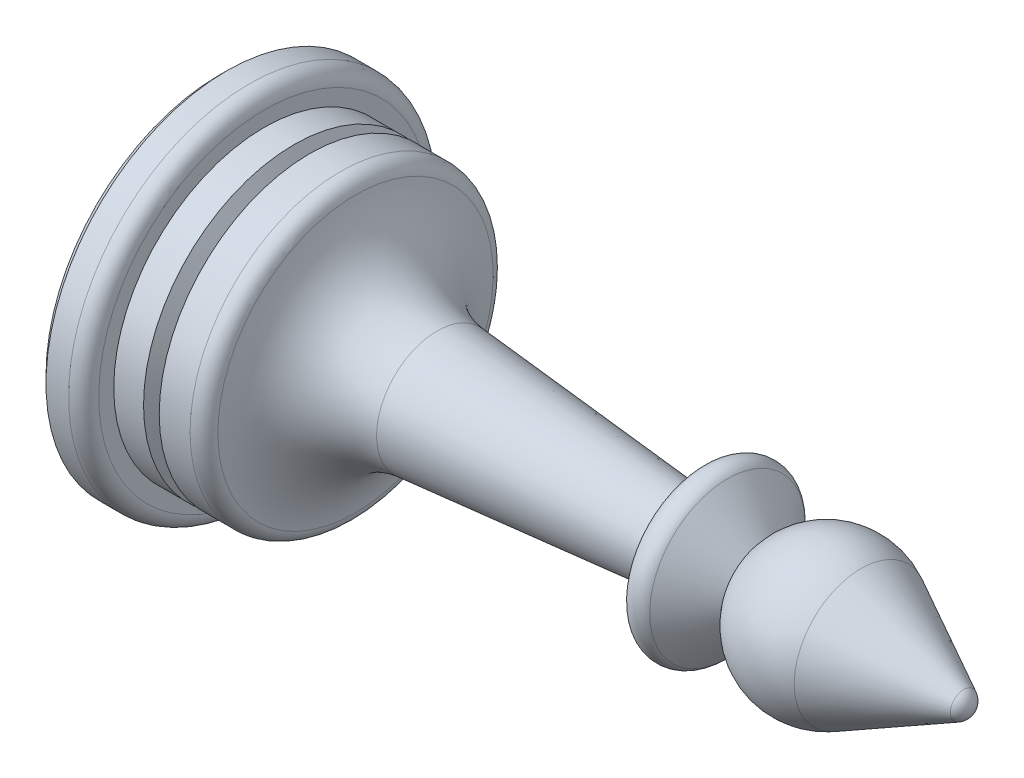
SolidWorks part; units mm, degrees
ref_plane "Front Plane" through (0, 0, 0) normal (0, 0, 1) x (1, 0, 0)
ref_plane "Top Plane" through (0, 0, 0) normal (0, 1, 0) x (1, 0, 0)
ref_plane "Right Plane" through (0, 0, 0) normal (1, 0, 0) x (0, 0, -1)
sketch "Sketch1" plane through (0, 0, 0) normal (0, 0, 1) x (1, 0, 0)
  line L0 (0, 0) -> (0, 11.5)
  line L1 (0.5, 12) -> (2, 12)
  line L2 (3, 11) -> (3, 10)
  line L3 (3, 10) -> (8.0718, 10)
  line L4 (14.4805, 4.0225) -> (32, 2.5)
  line L5 (32, 2.5) -> (32, 4.5195)
  line L6 (33.766, 5.1623) -> (36, 2.5)
  line L7 (0, 0) -> (50, 0)
  line L8 (0, 0) -> (-16.2845, 0) construction
  line L9 (50, 0) -> (50, -26.6806) construction
  line L10 (36, 2.5) -> (36, 27.3883) construction
  line L11 (36, 2.5) -> (48.7777, 27.0457) construction
  line L12 (36, 2.5) -> (23.2223, 27.0457) construction
  line L13 (23.2223, 27.0457) -> (48.7777, 27.0457) construction
  line L14 (0, 11.5) -> (0.5, 12)
  line L15 (42.637, 4.436) -> (49.4614, 0.8872)
  arc A0 (9.0615, 9.1429) -> (14.4805, 4.0225) centre (15, 10) ccw
  arc A1 (36, 2.5) -> (42.637, 4.436) centre (40.3301, 0) cw
  arc A2 (2, 12) -> (3, 11) centre (2, 11) cw
  arc A3 (8.0718, 10) -> (9.0615, 9.1429) centre (8.0718, 9) cw
  arc A4 (32, 4.5195) -> (33.766, 5.1623) centre (33, 4.5195) cw
  arc A5 (50, 0) -> (49.4614, 0.8872) centre (49, 0) ccw
  point P1 (0, 12)
  point P20 (3, 12)
  point P23 (9, 10)
  dimension "D1" = 5
  dimension "D8" = 55
  dimension "D13" = 6
  dimension "D14" = 1
  dimension "D15" = 1
  dimension "D2" = 24
  dimension "D3" = 3
  dimension "D4" = 20
  dimension "D5" = 6
  dimension "D6" = 5
  dimension "D7" = 50
  dimension "D9" = 50
  dimension "D10" = 27.5
  dimension "D11" = 14
  dimension "D12" = 18
revolve "Revolve1" add sketch "Sketch1" angle 360 about L7
sketch "Sketch2" plane through (0, 0, 0) normal (0, 0, 1) x (1, 0, 0)
  line L0 (4.9794, 10) -> (5.5, 9)
  line L1 (8.0718, 10) -> (3, 10) construction
  line L2 (5.5, 9) -> (6.0206, 10)
  line L3 (4.9794, 10) -> (6.0206, 10)
  line L4 (5.5, 9) -> (5.5, 10) construction
  line L5 (3, -10) -> (3, 10) construction
  line L6 (0, 0) -> (11.1779, 0) construction
  dimension "D1" = 55
  dimension "D2" = 1
  dimension "D3" = 2.5
revolve "Cut-Revolve1" cut sketch "Sketch2" angle 360 about L6
sketch "Sketch3" plane through (0, 0, 0) normal (-1, 0, 0) x (0, 0, 1)
  circle A0 centre (0, 0) radius 6
  dimension "D1" = 12
extrude "Cut-Extrude1" cut sketch "Sketch3" against normal blind 5
